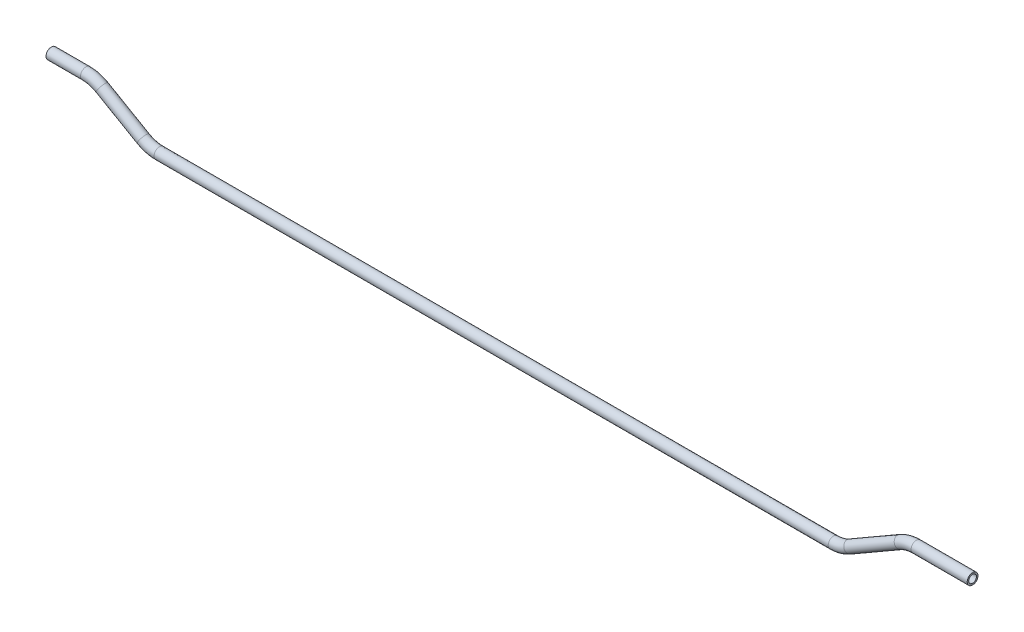
SolidWorks part; units mm, degrees
material "AISI 316 Stainless Steel Sheet (SS)"
ref_plane "Front Plane" through (0, 0, 0) normal (0, 0, 1) x (1, 0, 0)
ref_plane "Top Plane" through (0, 0, 0) normal (0, 1, 0) x (1, 0, 0)
ref_plane "Right Plane" through (0, 0, 0) normal (1, 0, 0) x (0, 0, -1)
sketch "Sketch1" plane through (0, 0, 0) normal (0, 0, 1) x (1, 0, 0)
  line L0 (-15.2008, -14.7829) -> (5.0948, -14.7829)
  line L1 (14.6198, -17.3351) -> (38.7742, -31.2807)
  line L2 (48.2992, -33.8329) -> (444.4903, -33.8329)
  line L3 (454.0153, -31.2807) -> (483.669, -14.1601)
  line L4 (493.194, -11.6079) -> (526.1896, -11.6079)
  line L5 (-15.2008, -14.7829) -> (5.0948, -14.7829) construction
  line L6 (5.0948, -14.7829) -> (34.3025, -14.7829) construction
  line L7 (38.7742, -31.2807) -> (14.6198, -17.3351) construction
  line L8 (14.6198, -17.3351) -> (-19.8781, 2.5823) construction
  line L9 (14.6198, -17.3351) -> (38.7742, -31.2807) construction
  line L10 (38.7742, -31.2807) -> (68.1833, -48.26) construction
  line L11 (444.4903, -33.8329) -> (48.2992, -33.8329) construction
  line L12 (48.2992, -33.8329) -> (3.7006, -33.8329) construction
  line L13 (48.2992, -33.8329) -> (444.4903, -33.8329) construction
  line L14 (444.4903, -33.8329) -> (161.3556, -33.8329) construction
  line L15 (483.669, -14.1601) -> (454.0153, -31.2807) construction
  line L16 (454.0153, -31.2807) -> (425.3133, -47.8518) construction
  line L17 (454.0153, -31.2807) -> (483.669, -14.1601) construction
  line L18 (483.669, -14.1601) -> (529.0056, 12.015) construction
  line L19 (526.1896, -11.6079) -> (493.194, -11.6079) construction
  line L20 (493.194, -11.6079) -> (418.7704, -11.6079) construction
  arc A0 (5.0948, -14.7829) -> (14.6198, -17.3351) centre (5.0948, -33.8329) cw
  arc A1 (38.7742, -31.2807) -> (48.2992, -33.8329) centre (48.2992, -14.7829) ccw
  arc A2 (444.4903, -33.8329) -> (454.0153, -31.2807) centre (444.4903, -14.7829) ccw
  arc A3 (483.669, -14.1601) -> (493.194, -11.6079) centre (493.194, -30.6579) cw
  point P13 (488.0896, -11.6079)
  point P24 (449.5948, -33.8329)
  point P25 (10.1992, -14.7829)
  point P26 (28.1359, 16.0867)
  point P27 (43.1948, -33.8329)
  dimension "D1" = 19.05
  dimension "D2" = 19.05
  dimension "D3" = 19.05
  dimension "D4" = 19.05
  dimension "D5" = 30
  dimension "D6" = 30
  dimension "D7" = 30
  dimension "D8" = 30
  dimension "D9" = 38.1
  dimension "D10" = 25.4
  dimension "D11" = 406.4
  dimension "D12" = 44.45
  dimension "D13" = 38.1
ref_plane "Plane1" through (-15.2008, -14.7829, 0) normal (1, 0, 0) x (0, 0, -1)
sketch "Sketch2" plane through (-15.2008, -14.7829, 0) normal (1, 0, 0) x (0, 0, -1)
  circle A0 centre (0, 0) radius 3.175
  circle A1 centre (0, 0) radius 2.286
  dimension "D1" = 4.572
  dimension "D2" = 6.35
sweep "Sweep1" add profiles "Sketch2" path "Sketch1"
